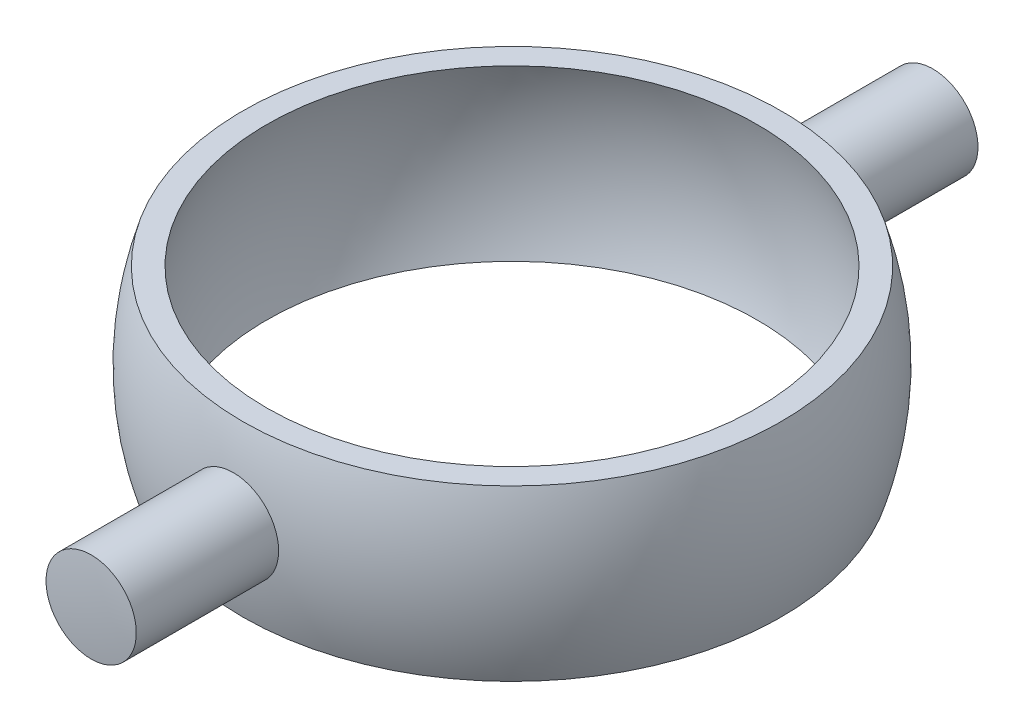
SolidWorks part; units mm, degrees
ref_plane "Front Plane" through (0, 0, 0) normal (0, 0, 1) x (1, 0, 0)
ref_plane "Top Plane" through (0, 0, 0) normal (0, 1, 0) x (1, 0, 0)
ref_plane "Right Plane" through (0, 0, 0) normal (1, 0, 0) x (0, 0, -1)
sketch "Sketch1" plane through (0, 0, 0) normal (0, 0, 1) x (1, 0, 0)
  line L0 (0, 8.2007) -> (0, 0) construction
  line L1 (0, 0) -> (-13.9073, 0) construction
  line L2 (-23.8485, 7.5) -> (-21.7428, 7.5)
  line L3 (-21.7428, -7.5) -> (-23.8485, -7.5)
  arc A0 (-21.7428, 7.5) -> (-21.7428, -7.5) centre (0, 0) ccw
  arc A1 (-23.8485, 7.5) -> (-23.8485, -7.5) centre (0, 0) ccw
  dimension "D2" = 25
  dimension "D3" = 23
  dimension "D1" = 15
  dimension "D4" = 13.9073
revolve "Revolve1" add sketch "Sketch1" angle 360 about L0
ref_plane "Plane1" through (0, 0, 37.5) normal (0, 0, 1) x (1, 0, 0)
sketch "Sketch3" plane through (0, 0, 37.5) normal (0, 0, 1) x (1, 0, 0)
  circle A0 centre (0, 0) radius 4
  dimension "8" = 8
extrude "Boss-Extrude1" add sketch "Sketch3" against normal up to surface (12.8221 mm away)
mirror "Mirror1" about plane through (0, 0, 0) normal (0, 0, 1) of "Boss-Extrude1"
sketch "Sketch4" plane through (0, 0, 0) normal (1, 0, 0) x (0, 0, -1)
  line L0 (0, 37.5) -> (0, 0) construction
  line L1 (0, 0) -> (-37.5, 0) construction
  line L2 (-37.5, 4) -> (-37.5, -4) construction
  line L3 (0, 40) -> (0, 37.5)
  line L4 (0, -37.5) -> (0, -40)
  arc A0 (0, 40) -> (0, -40) centre (0, 0) ccw
  arc A1 (0, 37.5) -> (0, -37.5) centre (0, 0) ccw
  dimension "D1" = 40
  dimension "D2" = 37.5
revolve "Cut-Revolve1" cut sketch "Sketch4" angle 360 about L0
